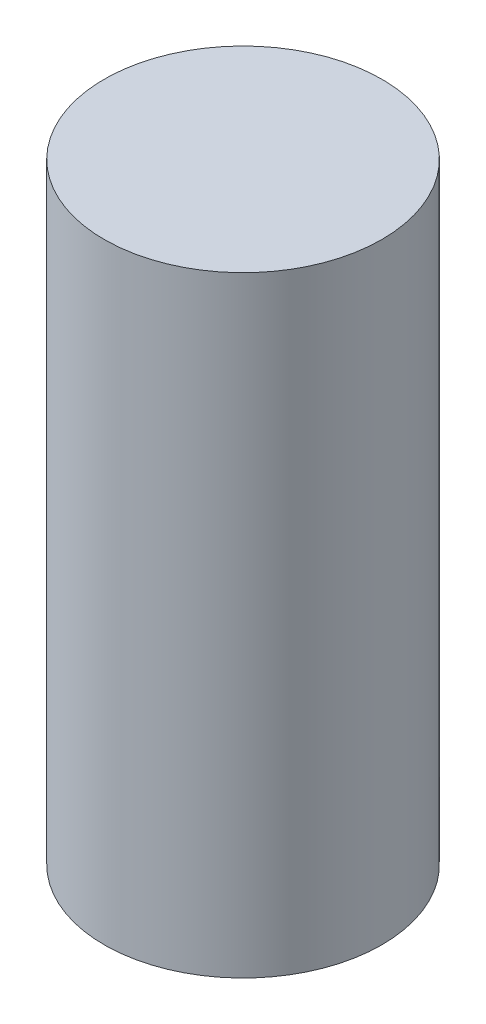
SolidWorks part; units mm, degrees
ref_plane "Front Plane" through (0, 0, 0) normal (0, 0, 1) x (1, 0, 0)
ref_plane "Top Plane" through (0, 0, 0) normal (0, 1, 0) x (1, 0, 0)
ref_plane "Right Plane" through (0, 0, 0) normal (1, 0, 0) x (0, 0, -1)
sketch "Sketch1" plane through (0, 0, 0) normal (0, 0, 1) x (1, 0, 0)
  line L0 (0, 18.161) -> (0, 23.4801) construction
  line L1 (-8.255, 18.161) -> (0, 18.161)
  line L2 (-8.255, 18.161) -> (-8.255, -18.161)
  line L3 (-8.255, -18.161) -> (0, -18.161)
  line L4 (0, 18.161) -> (0, -18.161)
  point P5 (0, 0)
  dimension "D1" = 16.51
  dimension "D2" = 36.322
revolve "Revolve1" add sketch "Sketch1" angle 360 about L0
